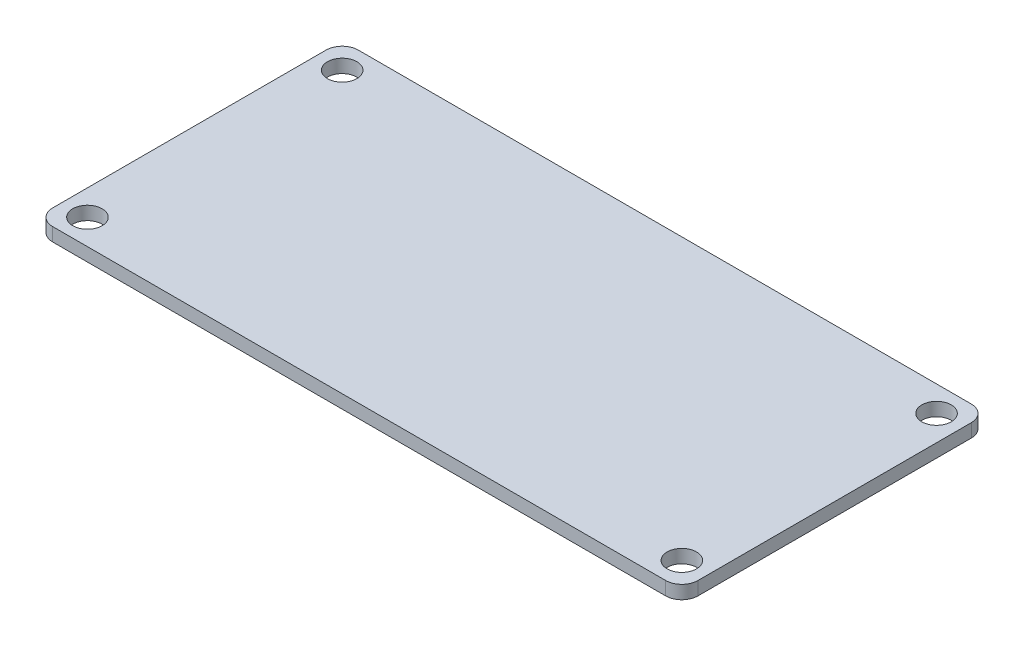
SolidWorks part; units mm, degrees
ref_plane "Front Plane" through (0, 0, 0) normal (0, 0, 1) x (1, 0, 0)
ref_plane "Top Plane" through (0, 0, 0) normal (0, 1, 0) x (1, 0, 0)
ref_plane "Right Plane" through (0, 0, 0) normal (1, 0, 0) x (0, 0, -1)
sketch "Sketch1" plane through (0, 0, 0) normal (0, 1, 0) x (1, 0, 0)
  line L1 (0, 0) -> (48.26, 0)
  line L2 (0, 0) -> (0, 22.86)
  line L3 (0, 22.86) -> (48.26, 22.86)
  line L4 (48.26, 0) -> (48.26, 22.86)
  dimension "D1" = 48.26
  dimension "D2" = 22.86
extrude "Boss-Extrude1" add sketch "Sketch1" along normal blind 1
sketch "Sketch2" plane through (0, 1, 0) normal (0, 1, 0) x (1, 0, 0)
  line L0 (0, 22.86) -> (0, 0) construction
  line L1 (0, 0) -> (48.26, 0) construction
  circle A0 centre (1.905, 20.955) radius 1.0998
  circle A1 centre (1.905, 1.905) radius 1.0998
  circle A2 centre (46.355, 1.905) radius 1.0998
  circle A3 centre (46.355, 20.955) radius 1.0998
  dimension "D1" = 2.1996
  dimension "D2" = 1.905
  dimension "D3" = 20.955
  dimension "D4" = 1.905
  dimension "D5" = 46.355
extrude "Cut-Extrude1" cut sketch "Sketch2" against normal through all both and the other way through all
fillet "Fillet1" radius 1.2065 4 edges at (48.26, 0.5, -22.86) (48.26, 0.5, 0) (0, 0.5, -22.86) (0, 0.5, 0)
sketch "Sketch3" plane through (0, 0, 0) normal (0, -1, 0) x (1, 0, 0)
  line L0 (0, -21.6535) -> (0, -1.2065) construction
  line L1 (5.1, -15.43) -> (-1, -15.43)
  line L2 (5.1, -15.43) -> (5.1, -7.43)
  line L3 (5.1, -7.43) -> (-1, -7.43)
  line L4 (-1, -15.43) -> (-1, -7.43)
  point P6 (-1, -11.43)
  point P7 (0, -11.43)
  dimension "D1" = 6.1
  dimension "D2" = 8
  dimension "D3" = 5.1
extrude "Boss-Extrude2" add sketch "Sketch3" along normal blind 3.5
